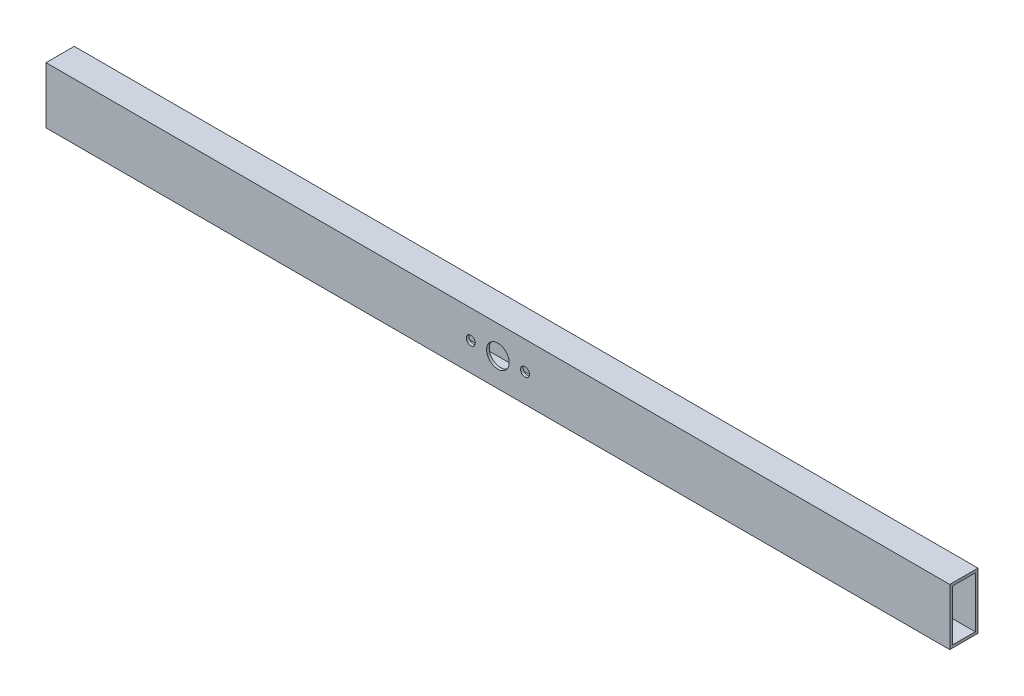
SolidWorks part; units mm, degrees
material "Stainless Steel (ferritic)"
ref_plane "Front Plane" through (0, 0, 0) normal (0, 0, 1) x (1, 0, 0)
ref_plane "Top Plane" through (0, 0, 0) normal (0, 1, 0) x (1, 0, 0)
ref_plane "Right Plane" through (0, 0, 0) normal (1, 0, 0) x (0, 0, -1)
sketch "Sketch1" plane through (0, 0, 0) normal (1, 0, 0) x (0, 0, -1)
  line L0 (-5.05, 11.3) -> (5.05, 11.3)
  line L1 (-6.25, -12.5) -> (6.25, -12.5)
  line L2 (-6.25, -12.5) -> (-6.25, 12.5)
  line L3 (-6.25, 12.5) -> (6.25, 12.5)
  line L4 (6.25, -12.5) -> (6.25, 12.5)
  line L5 (-6.25, -12.5) -> (6.25, 12.5) construction
  line L6 (-6.25, 12.5) -> (6.25, -12.5) construction
  line L7 (5.05, -11.3) -> (5.05, 11.3)
  line L8 (-5.05, -11.3) -> (5.05, -11.3)
  line L9 (-5.05, -11.3) -> (-5.05, 11.3)
  point P0 (0, 0)
  dimension "D1" = 12.5
  dimension "D2" = 25
  dimension "D3" = 1.2
extrude "Boss-Extrude1" add sketch "Sketch1" along normal blind 400
sketch "Sketch2" plane through (0, 0, -6.25) normal (0, 0, -1) x (-1, 0, 0)
  line L0 (-400, 12.5) -> (0, 12.5) construction
  line L1 (-200, 12.5) -> (-200, -12.5) construction
  line L2 (-400, -12.5) -> (0, -12.5) construction
  point P0 (-22, 0)
  point P3 (-378, 0)
  dimension "D1" = 12.5
  dimension "D2" = 12.5
  dimension "D3" = 178
  dimension "D4" = 178
sketch "Sketch3" plane through (0, 0, -6.25) normal (0, 0, -1) x (-1, 0, 0)
  line L0 (-200, 12.5) -> (-200, -12.5) construction
  line L1 (-400, -12.5) -> (0, -12.5) construction
  circle A0 centre (-200, 0) radius 5
  circle A1 centre (-188, 0) radius 2
  circle A2 centre (-212, 0) radius 2
  dimension "D1" = 10
  dimension "D2" = 4
  dimension "D3" = 4
  dimension "D4" = 12
  dimension "D5" = 12
  dimension "D6" = 12.5
  dimension "D7" = 12.5
extrude "Cut-Extrude1" cut sketch "Sketch3" against normal blind 20
